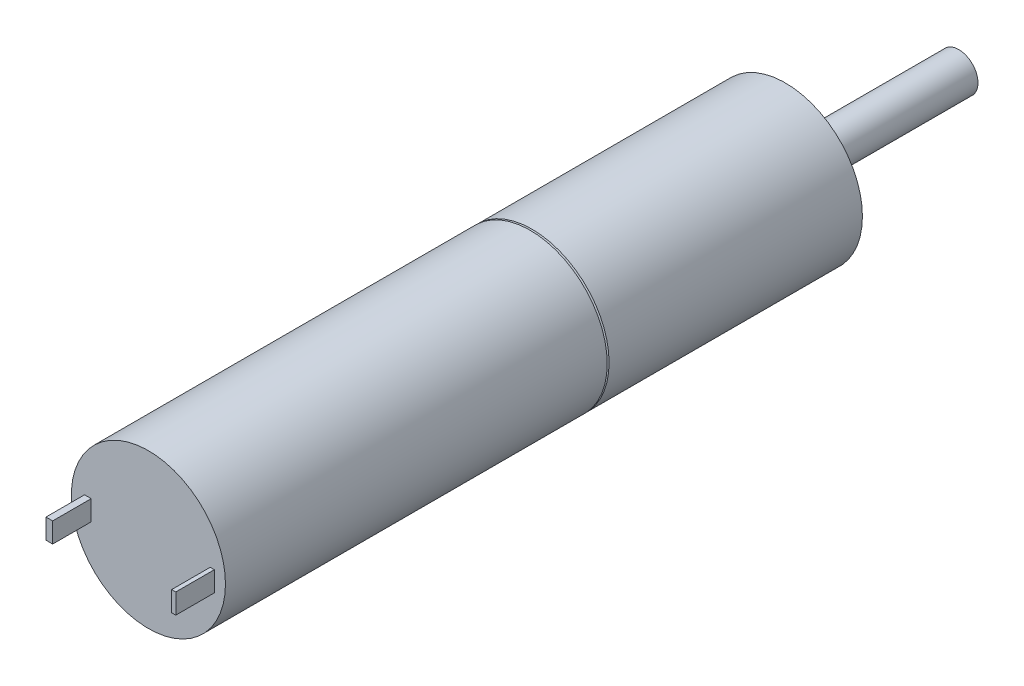
SolidWorks part; units mm, degrees
ref_plane "Front Plane" through (0, 0, 0) normal (0, 0, 1) x (1, 0, 0)
ref_plane "Top Plane" through (0, 0, 0) normal (0, 1, 0) x (1, 0, 0)
ref_plane "Right Plane" through (0, 0, 0) normal (1, 0, 0) x (0, 0, -1)
sketch "Sketch1" plane through (0, 0, 0) normal (0, 0, 1) x (1, 0, 0)
  circle A0 centre (0, 0) radius 6
  dimension "D1" = 12
extrude "Extrude1" add sketch "Sketch1" along normal blind 29.8 and the other way blind 19.8
sketch "Sketch2" plane through (0, 0, 29.8) normal (0, 0, 1) x (1, 0, 0)
  line L1 (4.8087, 0.5355) -> (5.1308, 0.5355)
  line L2 (4.8087, 0.5355) -> (4.8087, -1.0284)
  line L3 (4.8087, -1.0284) -> (5.1308, -1.0284)
  line L4 (5.1308, 0.5355) -> (5.1308, -1.0284)
  line L5 (-4.9748, 0.5355) -> (-4.4551, 0.5355)
  line L6 (-4.9748, 0.5355) -> (-4.9748, -1.0284)
  line L7 (-4.9748, -1.0284) -> (-4.4551, -1.0284)
  line L8 (-4.4551, 0.5355) -> (-4.4551, -1.0284)
extrude "Extrude2" add sketch "Sketch2" along normal blind 3
sketch "Sketch3" plane through (0, 0, -19.8) normal (0, 0, -1) x (-1, 0, 0)
  circle A0 centre (0, 0) radius 1.5
  dimension "D1" = 3
extrude "Extrude3" add sketch "Sketch3" along normal blind 13.5
sketch "Sketch4" plane through (0, 0, -19.8) normal (0, 0, -1) x (-1, 0, 0)
  line L0 (-4.75, 0) -> (4.75, 0) construction
  circle A0 centre (4.75, 0) radius 1
  circle A1 centre (-4.75, 0) radius 1
  point P4 (0, 0)
  dimension "D1" = 2
  dimension "D2" = 2
  dimension "D3" = 9.5
extrude "Cut-Extrude1" cut sketch "Sketch4" against normal blind 13.5
sketch "Sketch6" plane through (0, 0, 0) normal (1, 0, 0) x (0, 0, -1)
  line L1 (0, 5.8) -> (0.7148, 7.764)
  line L2 (0.7148, 7.764) -> (-0.7148, 7.764)
  line L3 (-0.7148, 7.764) -> (0, 5.8)
  line L4 (19.8, 6) -> (-29.8, 6) construction
  line L5 (0, 0) -> (-5.8629, 0) construction
  dimension "D1" = 0.2
revolve "Cut-Revolve1" cut sketch "Sketch6" angle 360 about L5
